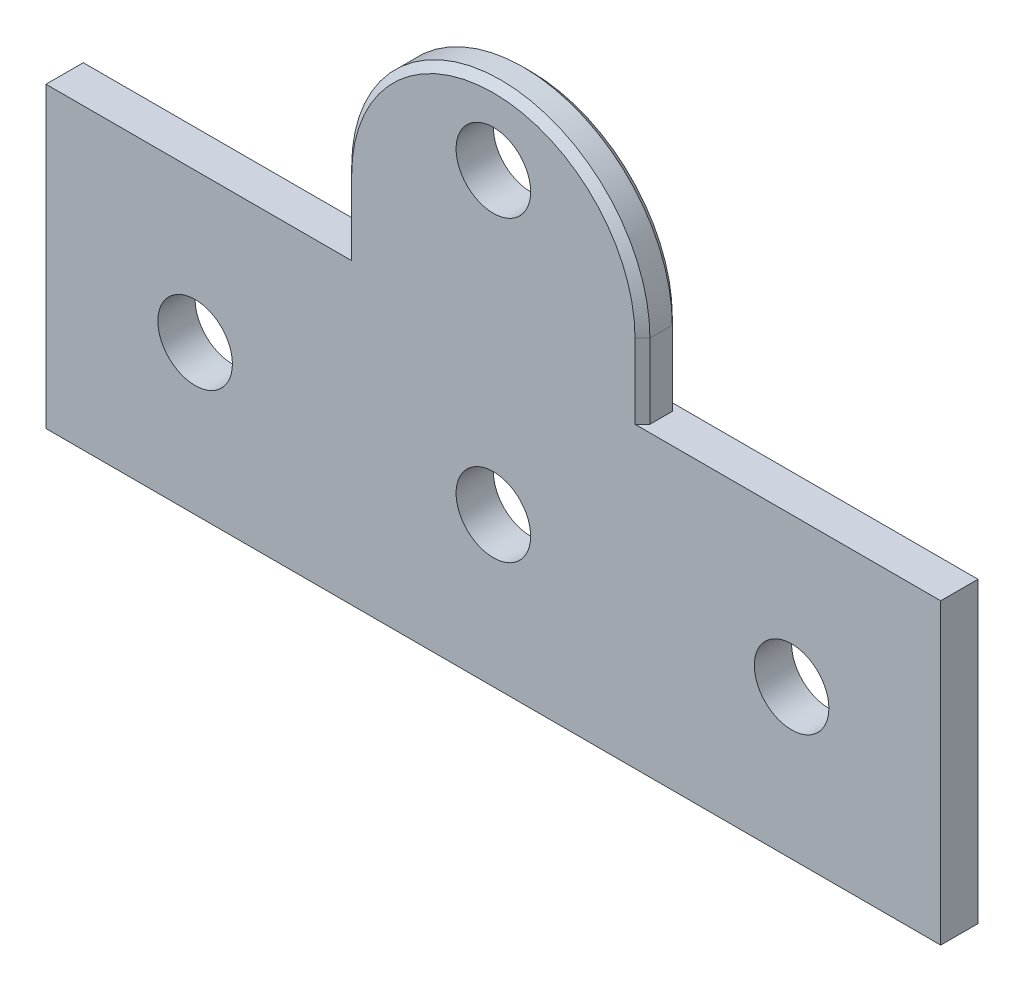
SolidWorks part; units mm, degrees
ref_plane "Front Plane" through (0, 0, 0) normal (0, 0, 1) x (1, 0, 0)
ref_plane "Top Plane" through (0, 0, 0) normal (0, 1, 0) x (1, 0, 0)
ref_plane "Right Plane" through (0, 0, 0) normal (1, 0, 0) x (0, 0, -1)
sketch "Sketch1" plane through (0, 0, 0) normal (0, 0, 1) x (1, 0, 0)
  line L0 (0, 25.4) -> (25.4, 25.4) construction
  line L1 (0, 0) -> (25.4, 0)
  line L5 (12.7, 44.45) -> (12.7, 0) construction
  line L6 (-40.1614, 44.45) -> (64.5079, 44.45) construction
  line L7 (0, 25.4) -> (0, 31.75)
  line L8 (25.4, 31.75) -> (25.4, 25.4)
  line L9 (0, 25.4) -> (-25.4, 25.4)
  line L10 (-25.4, 25.4) -> (-25.4, 0)
  line L11 (-25.4, 0) -> (0, 0)
  line L12 (25.4, 0) -> (50.8, 0)
  line L13 (50.8, 0) -> (50.8, 25.4)
  line L14 (50.8, 25.4) -> (25.4, 25.4)
  line L15 (-25.4, 12.7) -> (50.8, 12.7) construction
  circle A0 centre (12.7, 38.1) radius 3.175
  circle A1 centre (12.7, 38.1) radius 6.35 construction
  arc A2 (0, 31.75) -> (25.4, 31.75) centre (12.7, 31.75) cw
  circle A3 centre (12.7, 12.7) radius 3.175
  circle A4 centre (38.1, 12.7) radius 3.175
  circle A5 centre (-12.7, 12.7) radius 3.175
  dimension "D4" = 6.35
  dimension "D5" = 12.7
  dimension "D7" = 25.4
  dimension "D1" = 6.35
  dimension "D8" = 25.4
  dimension "D2" = 25.4
  dimension "D3" = 25.4
  dimension "D6" = 44.45
  dimension "D9" = 12.7
  dimension "D10" = 12.7
extrude "Boss-Extrude1" add sketch "Sketch1" along normal blind 3.175
chamfer "Chamfer2" distance 0.635 angle 45 6 edges at (25.4, 28.575, 0) (0, 28.575, 0) (12.7, 44.45, 0) (25.4, 28.575, 3.175) (0, 28.575, 3.175) (12.7, 44.45, 3.175)
